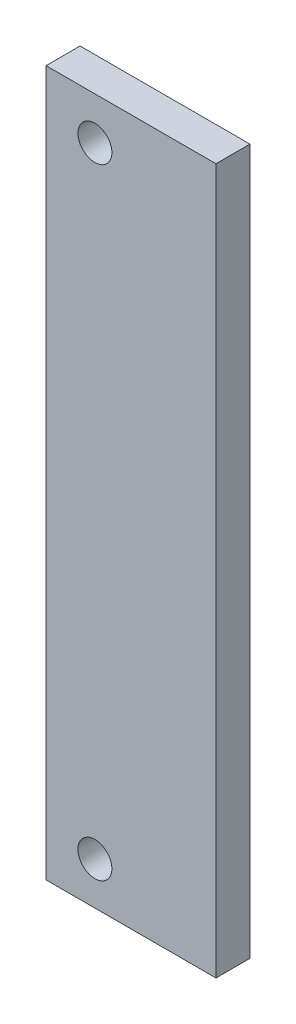
SolidWorks part; units mm, degrees
ref_plane "Front Plane" through (0, 0, 0) normal (0, 0, 1) x (1, 0, 0)
ref_plane "Top Plane" through (0, 0, 0) normal (0, 1, 0) x (1, 0, 0)
ref_plane "Right Plane" through (0, 0, 0) normal (1, 0, 0) x (0, 0, -1)
sketch "Sketch1" plane through (0, 0, 0) normal (0, 0, 1) x (1, 0, 0)
  line L1 (-20, -83) -> (20, -83)
  line L2 (-20, -83) -> (-20, 83)
  line L3 (-20, 83) -> (20, 83)
  line L4 (20, -83) -> (20, 83)
  line L5 (-20, -83) -> (20, 83) construction
  line L6 (-20, 83) -> (20, -83) construction
  point P0 (0, 0)
  dimension "D1" = 40
  dimension "D2" = 166
extrude "Boss-Extrude1" add sketch "Sketch1" along normal mid plane 8
sketch "Sketch2" plane through (0, 0, 4) normal (0, 0, 1) x (1, 0, 0)
  line L0 (0, 0) -> (-41.9743, 0) construction
  line L1 (20, -83) -> (20, 83) construction
  circle A0 centre (-8.5, 73) radius 4
  circle A2 centre (-8.5, -73) radius 4
  point P2 (0, 63.9835)
  point P3 (-7.4665, 63.8898)
  point P7 (-1.8561, 62.2856)
  point P8 (-1.4511, -59.3535)
  dimension "D1" = 28.5
  dimension "D2" = 8
  dimension "D3" = 146
extrude "Cut-Extrude1" cut sketch "Sketch2" against normal through all
